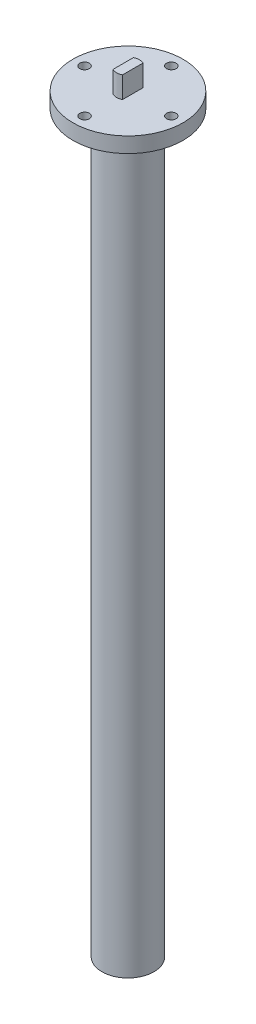
SolidWorks part; units mm, degrees
ref_plane "Front Plane" through (0, 0, 0) normal (0, 0, 1) x (1, 0, 0)
ref_plane "Top Plane" through (0, 0, 0) normal (0, 1, 0) x (1, 0, 0)
ref_plane "Right Plane" through (0, 0, 0) normal (1, 0, 0) x (0, 0, -1)
sketch "Sketch1" plane through (0, 0, 0) normal (0, 1, 0) x (1, 0, 0)
  circle A0 centre (0, 0) radius 22.86
  dimension "D1" = 45.72
extrude "Boss-Extrude1" add sketch "Sketch1" along normal blind 6.35
sketch "Sketch2" plane through (0, 6.35, 0) normal (0, 1, 0) x (1, 0, 0)
  line L0 (1.9685, 4.2668) -> (1.9685, -4.2668)
  line L1 (-1.9685, 4.2668) -> (-1.9685, -4.2668)
  line L2 (0, 0) -> (1.9685, 0) construction
  line L3 (0, 0) -> (-1.9685, 0) construction
  circle A0 centre (0, 0) radius 4.699
  dimension "D1" = 9.398
  dimension "D2" = 1.9685
  dimension "D3" = 1.9685
extrude "Boss-Extrude2" add sketch "Sketch2" along normal blind 8.89 contours L0 A0 L1
sketch "Sketch3" plane through (0, 0, 0) normal (0, -1, 0) x (1, 0, 0)
  circle A0 centre (0, 0) radius 10.795
  dimension "D1" = 21.59
extrude "Boss-Extrude3" add sketch "Sketch3" along normal blind 304.8
chamfer "Chamfer1" distance 3.81 angle 45 1 edges at (0, 0, -10.795)
sketch "Sketch4" plane through (0, 6.35, 0) normal (0, 1, 0) x (1, 0, 0)
  line L0 (0, 0) -> (0, 18) construction
  circle A0 centre (0, 0) radius 18 construction
  dimension "D1" = 36
hole_wizard "5/32 (0.15625) Diameter Hole1" positions "Sketch5" profile "Sketch6" hole size "5/32" standard "ANSI Inch" end condition up to next
sketch "Sketch5" plane through (0, 6.35, 0) normal (0, 1, 0) x (1, 0, 0)
  point P0 (0, 18)
sketch "Sketch6" plane through (0, 6.35, -18) normal (1, 0, 0) x (0, 0, 1)
  line L0 (0, 0) -> (0, 6.351)
  line L1 (0, 6.351) -> (1.9844, 6.351)
  line L2 (1.9844, 6.351) -> (1.9844, 0)
  line L5 (1.9844, 0) -> (0, 0)
  line L11 (0, -6.35) -> (0, 107.95) construction
  dimension "Thru Hole Dia." = 3.9688
  dimension "Thru Hole Depth" = 6.351
pattern_circular "CirPattern1" count 4 over 360 about axis through (0, 0, 0) along (0, 1, 0) of "5/32 (0.15625) Diameter Hole1"
equation "\"D2@Sketch2\"=(.37-.215)/2"
